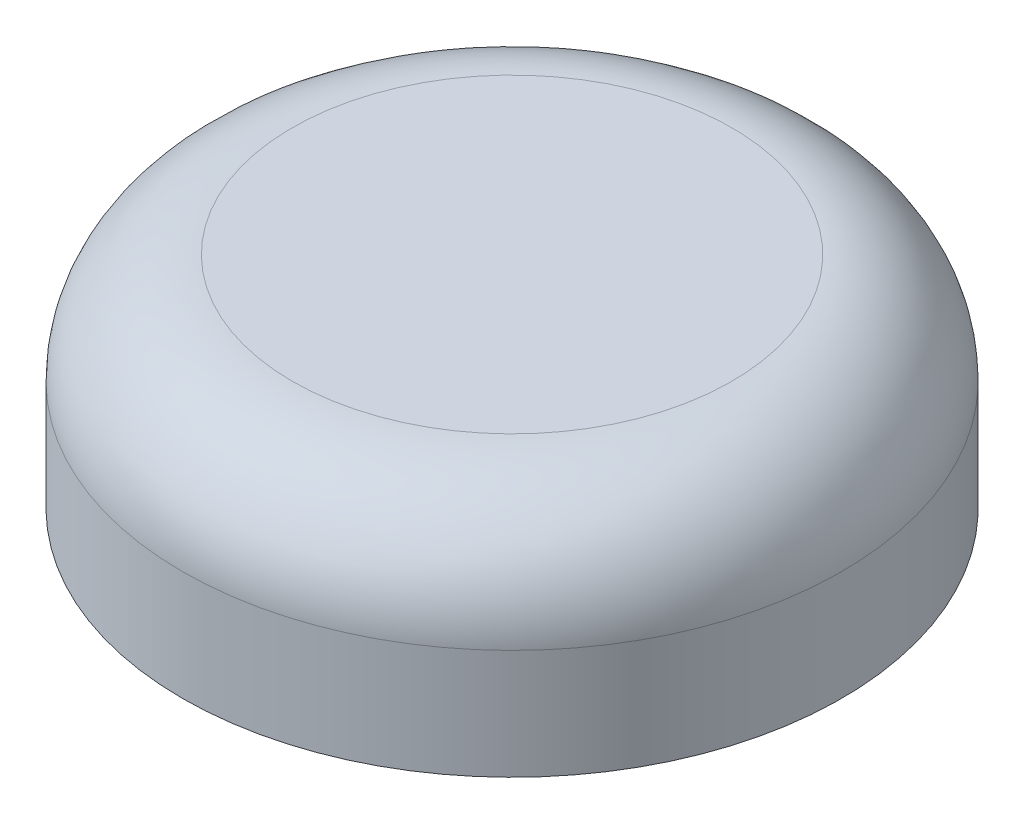
SolidWorks part; units mm, degrees
ref_plane "Front Plane" through (0, 0, 0) normal (0, 0, 1) x (1, 0, 0)
ref_plane "Top Plane" through (0, 0, 0) normal (0, 1, 0) x (1, 0, 0)
ref_plane "Right Plane" through (0, 0, 0) normal (1, 0, 0) x (0, 0, -1)
sketch "Sketch1" plane through (0, 0, 0) normal (0, 1, 0) x (1, 0, 0)
  line L2 (-2.5, 26.8794) -> (-2.5, 17.7149)
  line L4 (2.5, 26.8794) -> (2.5, 17.7149)
  arc A0 (-2.5, 19.8431) -> (2.5, 19.8431) centre (0, 0) ccw
  circle A1 centre (0, 0) radius 15
  arc A2 (-2.5, 24.8747) -> (2.5, 24.8747) centre (0, 0) ccw
  circle A3 centre (0, 0) radius 30
  dimension "D1" = 40
  dimension "D2" = 30
  dimension "D3" = 50
  dimension "D4" = 60
  dimension "D5" = 2.5
  dimension "D6" = 5
extrude "Boss-Extrude1" add sketch "Sketch1" along normal blind 10
sketch "Sketch2" plane through (0, 10, 0) normal (0, 1, 0) x (1, 0, 0)
  circle A0 centre (0, 0) radius 30
extrude "Boss-Extrude2" add sketch "Sketch2" along normal blind 10
fillet "Fillet1" radius 10 1 edges at (0, 20, 30)
